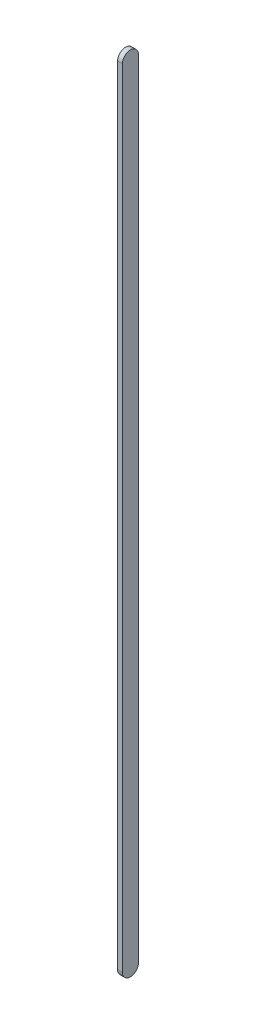
SolidWorks part; units mm, degrees
ref_plane "Front Plane" through (0, 0, 0) normal (0, 0, 1) x (1, 0, 0)
ref_plane "Top Plane" through (0, 0, 0) normal (0, 1, 0) x (1, 0, 0)
ref_plane "Right Plane" through (0, 0, 0) normal (1, 0, 0) x (0, 0, -1)
sketch "Sketch1" plane through (0, 0, 0) normal (1, 0, 0) x (0, 0, -1)
  line L0 (0, 0) -> (0, -490) construction
  line L1 (0, -490) -> (0, 0) construction
  line L2 (-5, -490) -> (-5, 0)
  line L3 (5, -490) -> (5, 0)
  arc A0 (-5, -490) -> (5, -490) centre (0, -490) ccw
  arc A1 (5, 0) -> (-5, 0) centre (0, 0) ccw
  point P3 (0, -245)
  dimension "D2" = 5
  dimension "D1" = 490
extrude "Boss-Extrude1" add sketch "Sketch1" along normal blind 3 contours L3 A1 L2 A0
